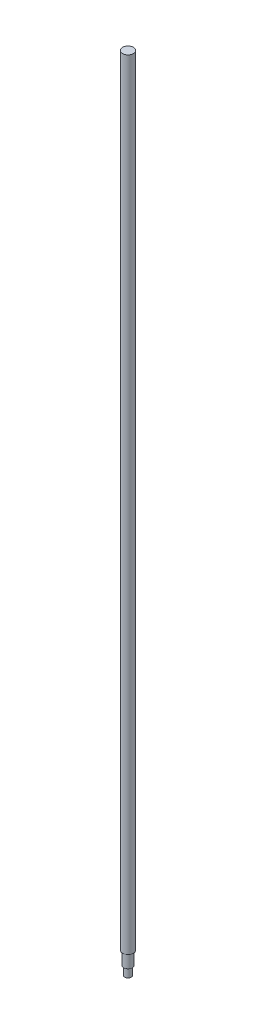
SolidWorks part; units mm, degrees
ref_plane "Front Plane" through (0, 0, 0) normal (0, 0, 1) x (1, 0, 0)
ref_plane "Top Plane" through (0, 0, 0) normal (0, 1, 0) x (1, 0, 0)
ref_plane "Right Plane" through (0, 0, 0) normal (1, 0, 0) x (0, 0, -1)
sketch "Sketch1" plane through (0, 0, 0) normal (0, 1, 0) x (1, 0, 0)
  circle A0 centre (0, 0) radius 7.5
extrude "Boss-Extrude1" add sketch "Sketch1" along normal blind 1070
thread "Thread1" pitch 2 start angle 0, offset 0, length 900, pitch 2, diameter 16
ref_plane "Plane1" through (-8, 1080, 0) normal (0, 0, 1) x (-1, 0, 0)
sketch "Thread Profile1" plane through (-8, 1080, 0) normal (0, 0, 1) x (-1, 0, 0)
  line L0 (0, 0) -> (0, 2) construction
  line L11 (0, 0) -> (0, 1.75)
  line L12 (0, 1.75) -> (-1.0825, 1.125)
  line L13 (-1.0825, 1.125) -> (-1.0825, 0.625)
  line L15 (-1.0825, 0.625) -> (0, 0)
  line L17 (-1.0825, 0.875) -> (0, 0.875) construction
  point P2 (0, 0)
  dimension "Pitch" = 2
  dimension "Profile_Angle" = 60
  dimension "Profile_Land" = 0.5
  dimension "Profile_Height" = 1.0825
sketch "Эскиз1" plane through (0, 0, 0) normal (0, -1, 0) x (1, 0, 0)
  circle A0 centre (0, 0) radius 6
extrude "Бобышка-Вытянуть1" add sketch "Эскиз1" along normal blind 18
sketch "Эскиз2" plane through (0, -18, 0) normal (0, -1, 0) x (1, 0, 0)
  circle A0 centre (0, 0) radius 4.5
extrude "Бобышка-Вытянуть2" add sketch "Эскиз2" along normal blind 12
